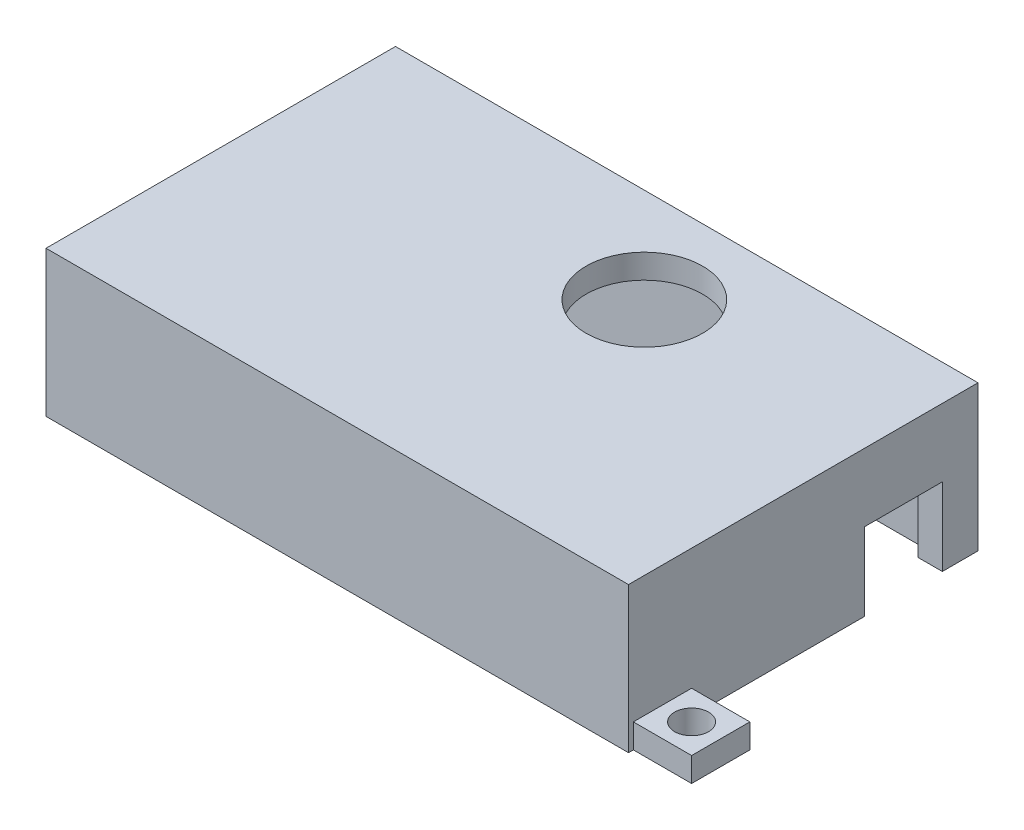
SolidWorks part; units mm, degrees
ref_plane "Front Plane" through (0, 0, 0) normal (0, 0, 1) x (1, 0, 0)
ref_plane "Top Plane" through (0, 0, 0) normal (0, 1, 0) x (1, 0, 0)
ref_plane "Right Plane" through (0, 0, 0) normal (1, 0, 0) x (0, 0, -1)
sketch "Sketch2" plane through (0, 0, 0) normal (0, 1, 0) x (1, 0, 0)
  line L5 (30, 18) -> (-30, 18)
  line L11 (30, 18) -> (30, -18)
  line L12 (30, -18) -> (-30, -18)
  line L14 (-30, 18) -> (-30, -18)
  line L18 (30, 18) -> (-30, -18) construction
  line L19 (30, -18) -> (-30, 18) construction
  point P0 (0, 0)
  dimension "D1" = 36
  dimension "D2" = 60
extrude "Boss-Extrude2" add sketch "Sketch2" along normal blind 15
sketch "Sketch5" plane through (0, 0, 0) normal (0, 1, 0) x (1, 0, 0)
  line L1 (27.5, -15.5) -> (-27.5, -15.5)
  line L2 (27.5, -15.5) -> (27.5, 15.5)
  line L3 (27.5, 15.5) -> (-27.5, 15.5)
  line L4 (-27.5, -15.5) -> (-27.5, 15.5)
  line L5 (27.5, -15.5) -> (-27.5, 15.5) construction
  line L6 (27.5, 15.5) -> (-27.5, -15.5) construction
  point P0 (0, 0)
  dimension "D1" = 31
  dimension "D2" = 55
extrude "Cut-Extrude1" cut sketch "Sketch5" along normal blind 12.5
sketch "Sketch6" plane through (0, 0, 0) normal (0, 1, 0) x (1, 0, 0)
  line L0 (-33, 12) -> (-33, 18)
  line L1 (-30, 18) -> (-36, 18)
  line L2 (-36, 18) -> (-36, 12)
  line L3 (-30, 18) -> (-30, 12)
  line L4 (33, -17.5) -> (33, -11.5)
  line L5 (-30, 18) -> (-30, -18) construction
  line L6 (-30, 12) -> (-36, 12)
  line L12 (30, -17.5) -> (36, -17.5)
  line L13 (36, -17.5) -> (36, -11.5)
  line L14 (30, -11.5) -> (36, -11.5)
  line L15 (30, -17.5) -> (30, -11.5)
  circle A0 centre (-33, 15) radius 1.75
  circle A2 centre (33, -14.5) radius 1.75
  point P6 (-33, 15)
  dimension "D3" = 3.5
  dimension "D4" = 3.5
  dimension "D1" = 6
  dimension "D2" = 6
extrude "Boss-Extrude3" add sketch "Sketch6" along normal blind 2.5 contours L4 A2 | L4 A2 | L0 A0 | L0 A0 | L14 L13 L12 L15 | L1 L2 L6 L3
sketch "Sketch7" plane through (0, 0, 0) normal (0, 1, 0) x (1, 0, 0)
  circle A6 centre (5.4047, 8.2267) radius 6
extrude "Cut-Extrude2" cut sketch "Sketch7" along normal blind 15
sketch "Sketch8" plane through (0, 0, 0) normal (0, 1, 0) x (1, 0, 0)
  line L6 (27.5, -15.5) -> (-17.5, -15.5)
  line L7 (27.5, -15.5) -> (27.5, 2.5)
  line L8 (27.5, 2.5) -> (-17.5, 2.5)
  line L9 (-17.5, -15.5) -> (-17.5, 2.5)
  line L10 (-21.0355, 6.5355) -> (-21.0355, 0)
  line L11 (-21.0355, 0) -> (-17.5, 0)
  line L12 (-21.0355, 6.5355) -> (-14.448, 6.5355)
  line L13 (-14.448, 6.5355) -> (-14.448, 2.5)
  dimension "D1" = 45
  dimension "D2" = 18
extrude "Boss-Extrude4" add sketch "Sketch8" along normal blind 12.5 contours L13 L12 L10 L11 L9 L8
ref_plane "Plane6" through (30, 0, 0) normal (1, 0, 0) x (0, 0, -1)
sketch "Sketch10" plane through (30, 0, 0) normal (1, 0, 0) x (0, 0, -1)
  line L0 (6.3271, 0) -> (14.3271, 0)
  line L1 (14.3271, 0) -> (14.3271, 8)
  line L2 (14.3271, 8) -> (6.3271, 8)
  line L3 (6.3271, 8) -> (6.3271, 0)
  line L4 (-11.5, 0) -> (18, 0) construction
  dimension "D1" = 8
  dimension "D2" = 8
extrude "Cut-Extrude3" cut sketch "Sketch10" against normal blind 12.5
